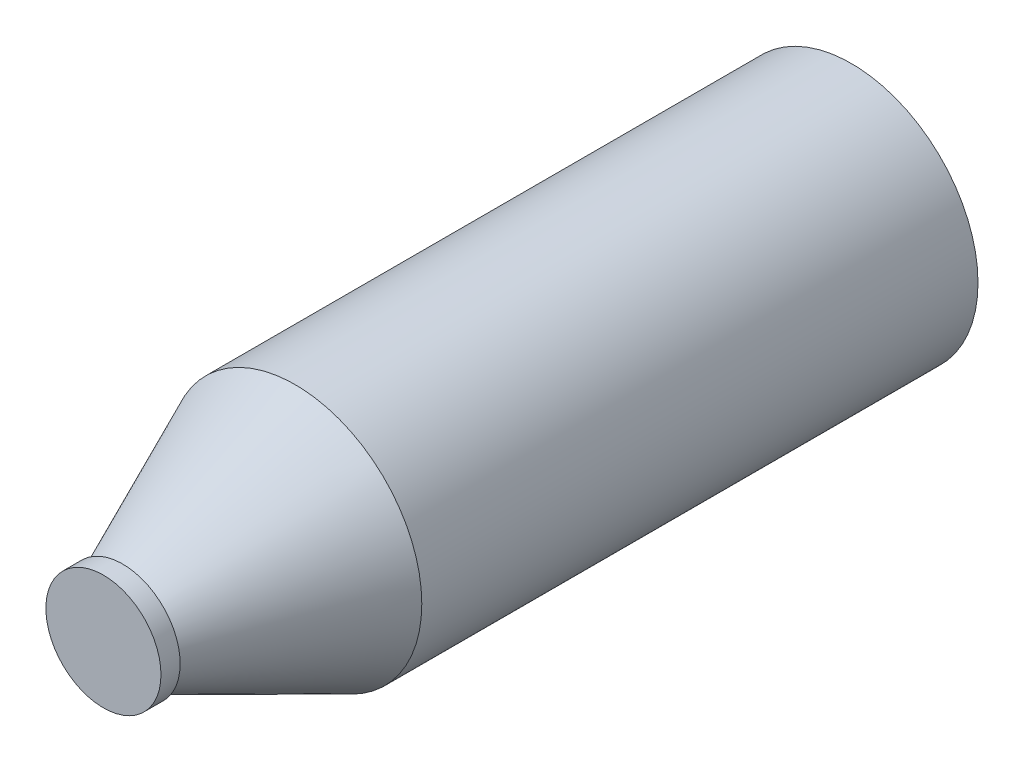
SolidWorks part; units mm, degrees
ref_plane "Plan de face" through (0, 0, 0) normal (0, 0, 1) x (1, 0, 0)
ref_plane "Plan de dessus" through (0, 0, 0) normal (0, 1, 0) x (1, 0, 0)
ref_plane "Plan de droite" through (0, 0, 0) normal (1, 0, 0) x (0, 0, -1)
sketch "Esquisse2" plane through (0, 0, 0) normal (0, 0, 1) x (1, 0, 0)
  circle A0 centre (41.0507, 36.4788) radius 33
  dimension "D1" = 66
extrude "Boss.-Extru.1" add sketch "Esquisse2" along normal blind 145
sketch "Esquisse4" plane through (0, 0, 145) normal (0, 0, 1) x (1, 0, 0)
  circle A0 centre (41.0507, 36.4788) radius 33
extrude "Boss.-Extru.2" add sketch "Esquisse4" along normal blind 45 draft 24
sketch "Esquisse5" plane through (0, 0, 190) normal (0, 0, 1) x (1, 0, 0)
  circle A0 centre (41.0507, 36.4788) radius 15
extrude "Boss.-Extru.3" add sketch "Esquisse5" along normal blind 5
